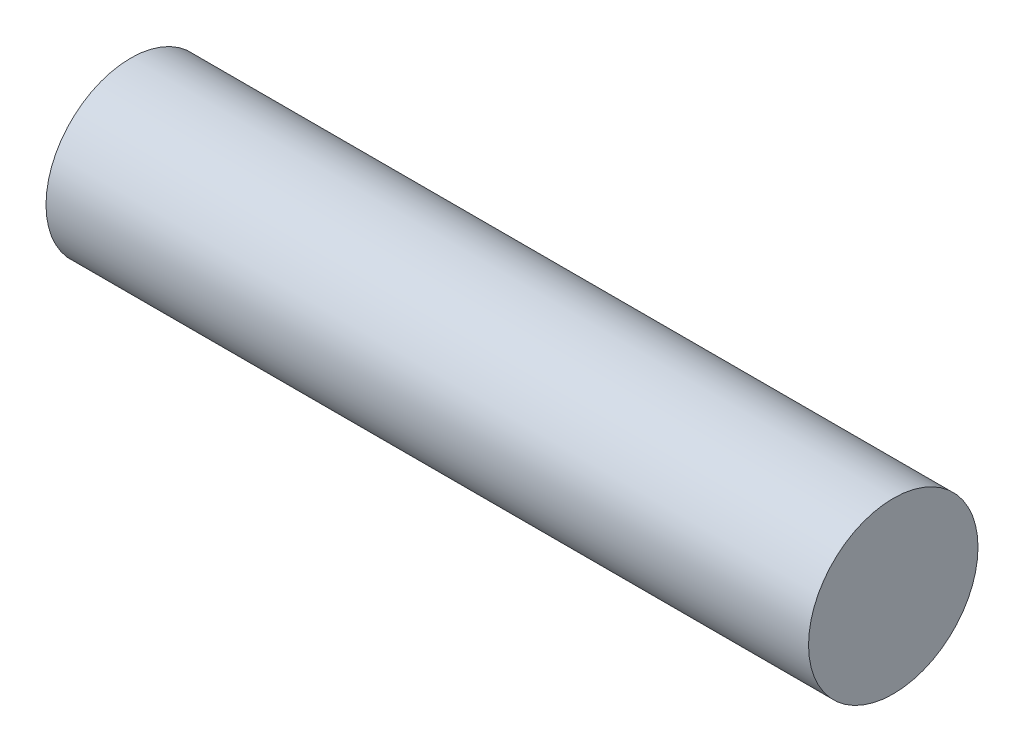
SolidWorks part; units mm, degrees
ref_plane "Front Plane" through (0, 0, 0) normal (0, 0, 1) x (1, 0, 0)
ref_plane "Top Plane" through (0, 0, 0) normal (0, 1, 0) x (1, 0, 0)
ref_plane "Right Plane" through (0, 0, 0) normal (1, 0, 0) x (0, 0, -1)
sketch "Sketch2" plane through (0, 0, 0) normal (1, 0, 0) x (0, 0, -1)
  circle A0 centre (0, 0) radius 1
  dimension "D1" = 2
extrude "Boss-Extrude1" add sketch "Sketch2" along normal blind 9
ref_plane "Plane1" through (9, 0, 0) normal (1, 0, 0) x (0, 0, -1)
ref_plane "Plane2" through (9, 0, 0) normal (1, 0, 0) x (0, 0, -1)
